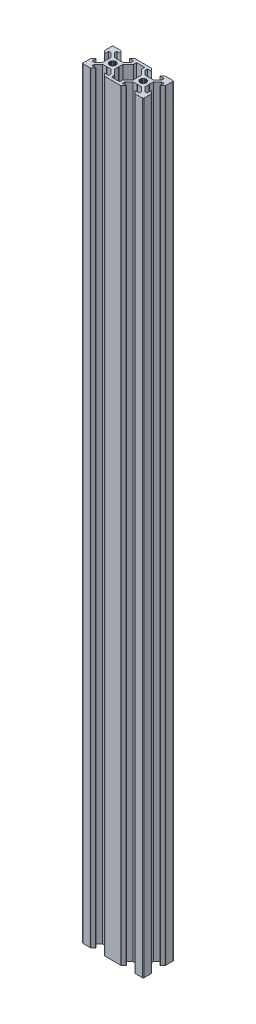
SolidWorks part; units mm, degrees
ref_plane "Alzado" through (0, 0, 0) normal (0, 0, 1) x (1, 0, 0)
ref_plane "Planta" through (0, 0, 0) normal (0, 1, 0) x (1, 0, 0)
ref_plane "Vista lateral" through (0, 0, 0) normal (1, 0, 0) x (0, 0, -1)
sketch "Croquis1" plane through (0, 0, 0) normal (0, 1, 0) x (1, 0, 0)
  line L0 (665.6997, 63.4231) -> (665.6997, 66.0554)
  line L1 (669.9997, 71.7624) -> (668.3603, 71.7624)
  line L2 (631.7997, 57.7624) -> (631.7997, 61.431)
  line L3 (631.801, 61.4707) -> (631.7997, 61.431)
  line L4 (631.8049, 61.5102) -> (631.801, 61.4707)
  line L5 (631.8113, 61.5494) -> (631.8049, 61.5102)
  line L6 (631.8204, 61.5881) -> (631.8113, 61.5494)
  line L7 (631.8319, 61.6261) -> (631.8204, 61.5881)
  line L8 (631.8459, 61.6633) -> (631.8319, 61.6261)
  line L9 (631.8623, 61.6995) -> (631.8459, 61.6633)
  line L10 (631.881, 61.7345) -> (631.8623, 61.6995)
  line L11 (631.902, 61.7682) -> (631.881, 61.7345)
  line L12 (631.9251, 61.8005) -> (631.902, 61.7682)
  line L13 (631.9503, 61.8312) -> (631.9251, 61.8005)
  line L14 (631.9775, 61.8602) -> (631.9503, 61.8312)
  line L15 (631.9775, 61.8602) -> (633.493, 63.3758)
  line L16 (633.493, 63.3758) -> (633.5997, 63.3758)
  line L17 (633.5997, 63.3758) -> (633.5997, 60.7624)
  line L18 (633.5997, 60.7624) -> (635.239, 60.7624)
  line L19 (635.239, 60.7624) -> (637.8997, 63.4231)
  line L20 (637.8997, 63.4231) -> (637.8997, 66.0554)
  line L21 (637.8997, 66.0554) -> (638.1067, 66.2624)
  line L22 (637.8997, 66.4694) -> (638.1067, 66.2624)
  line L23 (637.8997, 69.1018) -> (637.8997, 66.4694)
  line L24 (637.8997, 69.1018) -> (635.239, 71.7624)
  line L25 (633.5997, 71.7624) -> (635.239, 71.7624)
  line L26 (633.5997, 69.149) -> (633.5997, 71.7624)
  line L27 (633.493, 69.149) -> (633.5997, 69.149)
  line L28 (633.493, 69.149) -> (631.9775, 70.6646)
  line L29 (631.9775, 70.6646) -> (631.9503, 70.6936)
  line L30 (631.9503, 70.6936) -> (631.9251, 70.7243)
  line L31 (631.9251, 70.7243) -> (631.902, 70.7566)
  line L32 (633.2997, 56.2624) -> (636.8997, 56.2624)
  line L33 (631.902, 70.7566) -> (631.881, 70.7903)
  line L34 (637.0079, 56.2637) -> (636.8997, 56.2624)
  line L35 (631.881, 70.7903) -> (631.8623, 70.8254)
  line L36 (637.0475, 56.2676) -> (637.0079, 56.2637)
  line L37 (631.8623, 70.8254) -> (631.8459, 70.8616)
  line L38 (637.0867, 56.2741) -> (637.0475, 56.2676)
  line L39 (631.8459, 70.8616) -> (631.8319, 70.8987)
  line L40 (637.1253, 56.2831) -> (637.0867, 56.2741)
  line L41 (631.8319, 70.8987) -> (631.8204, 70.9368)
  line L42 (637.1634, 56.2946) -> (637.1253, 56.2831)
  line L43 (631.8204, 70.9368) -> (631.8113, 70.9754)
  line L44 (637.2005, 56.3086) -> (637.1634, 56.2946)
  line L45 (631.8113, 70.9754) -> (631.8049, 71.0146)
  line L46 (637.2367, 56.325) -> (637.2005, 56.3086)
  line L47 (631.8049, 71.0146) -> (631.801, 71.0542)
  line L48 (637.2718, 56.3438) -> (637.2367, 56.325)
  line L49 (631.801, 71.0542) -> (631.7997, 71.0939)
  line L50 (637.3055, 56.3647) -> (637.2718, 56.3438)
  line L51 (631.7997, 74.7624) -> (631.7997, 71.0939)
  line L52 (637.3378, 56.3879) -> (637.3055, 56.3647)
  line L53 (637.3685, 56.4131) -> (637.3378, 56.3879)
  line L54 (637.3975, 56.4402) -> (637.3685, 56.4131)
  line L55 (638.913, 57.9558) -> (637.3975, 56.4402)
  line L56 (638.913, 57.9558) -> (638.913, 58.0624)
  line L57 (638.913, 58.0624) -> (636.2997, 58.0624)
  line L58 (636.2997, 58.0624) -> (636.2997, 59.7018)
  line L59 (636.2997, 59.7018) -> (638.9603, 62.3624)
  line L60 (638.9603, 62.3624) -> (641.5998, 62.3624)
  line L61 (641.7997, 62.5623) -> (641.5998, 62.3624)
  line L62 (641.7997, 62.5623) -> (641.9995, 62.3624)
  line L63 (641.9995, 62.3624) -> (644.639, 62.3624)
  line L64 (647.2997, 59.7018) -> (644.639, 62.3624)
  line L65 (633.2997, 76.2624) -> (636.9682, 76.2624)
  line L66 (647.2997, 58.0624) -> (647.2997, 59.7018)
  line L67 (637.0079, 76.2611) -> (636.9682, 76.2624)
  line L68 (644.6863, 58.0624) -> (647.2997, 58.0624)
  line L69 (637.0475, 76.2572) -> (637.0079, 76.2611)
  line L70 (644.6863, 57.9558) -> (644.6863, 58.0624)
  line L71 (637.0867, 76.2508) -> (637.0475, 76.2572)
  line L72 (646.2019, 56.4402) -> (644.6863, 57.9558)
  line L73 (637.1253, 76.2417) -> (637.0867, 76.2508)
  line L74 (646.2019, 56.4402) -> (646.2309, 56.4131)
  line L75 (637.1634, 76.2302) -> (637.1253, 76.2417)
  line L76 (637.2005, 76.2162) -> (637.1634, 76.2302)
  line L77 (646.2309, 56.4131) -> (646.2616, 56.3879)
  line L78 (646.2616, 56.3879) -> (646.2939, 56.3647)
  line L79 (637.2367, 76.1998) -> (637.2005, 76.2162)
  line L80 (646.2939, 56.3647) -> (646.3276, 56.3438)
  line L81 (637.2718, 76.1811) -> (637.2367, 76.1998)
  line L82 (646.3276, 56.3438) -> (646.3626, 56.325)
  line L83 (637.3055, 76.1601) -> (637.2718, 76.1811)
  line L84 (646.3626, 56.325) -> (646.3988, 56.3086)
  line L85 (637.3378, 76.137) -> (637.3055, 76.1601)
  line L86 (646.3988, 56.3086) -> (646.436, 56.2946)
  line L87 (637.3685, 76.1118) -> (637.3378, 76.137)
  line L88 (646.436, 56.2946) -> (646.474, 56.2831)
  line L89 (637.3975, 76.0846) -> (637.3685, 76.1118)
  line L90 (646.474, 56.2831) -> (646.5127, 56.2741)
  line L91 (637.3975, 76.0846) -> (638.913, 74.569)
  line L92 (646.5127, 56.2741) -> (646.5519, 56.2676)
  line L93 (638.913, 74.569) -> (638.913, 74.4624)
  line L94 (646.5519, 56.2676) -> (646.5914, 56.2637)
  line L95 (638.913, 74.4624) -> (636.2997, 74.4624)
  line L96 (646.5914, 56.2637) -> (646.6997, 56.2624)
  line L97 (636.2997, 74.4624) -> (636.2997, 72.8231)
  line L98 (646.6997, 56.2624) -> (656.8997, 56.2624)
  line L99 (636.2997, 72.8231) -> (638.9603, 70.1624)
  line L100 (657.0079, 56.2637) -> (656.8997, 56.2624)
  line L101 (638.9603, 70.1624) -> (641.5998, 70.1624)
  line L102 (657.0475, 56.2676) -> (657.0079, 56.2637)
  line L103 (641.7997, 69.9626) -> (641.5998, 70.1624)
  line L104 (657.0867, 56.2741) -> (657.0475, 56.2676)
  line L105 (641.7997, 69.9626) -> (641.9995, 70.1624)
  line L106 (657.1253, 56.2831) -> (657.0867, 56.2741)
  line L107 (644.639, 70.1624) -> (641.9995, 70.1624)
  line L108 (657.1634, 56.2946) -> (657.1253, 56.2831)
  line L109 (647.2997, 72.8231) -> (644.639, 70.1624)
  line L110 (647.2997, 74.4624) -> (647.2997, 72.8231)
  line L111 (657.2005, 56.3086) -> (657.1634, 56.2946)
  line L112 (657.2367, 56.325) -> (657.2005, 56.3086)
  line L113 (644.6863, 74.4624) -> (647.2997, 74.4624)
  line L114 (657.2718, 56.3438) -> (657.2367, 56.325)
  line L115 (644.6863, 74.569) -> (644.6863, 74.4624)
  line L116 (657.3055, 56.3647) -> (657.2718, 56.3438)
  line L117 (644.6863, 74.569) -> (646.2019, 76.0846)
  line L118 (657.3378, 56.3879) -> (657.3055, 56.3647)
  line L119 (646.2019, 76.0846) -> (646.2309, 76.1118)
  line L120 (657.3685, 56.4131) -> (657.3378, 56.3879)
  line L121 (646.2309, 76.1118) -> (646.2616, 76.137)
  line L122 (657.3975, 56.4402) -> (657.3685, 56.4131)
  line L123 (646.2616, 76.137) -> (646.2939, 76.1601)
  line L124 (657.3975, 56.4402) -> (658.913, 57.9558)
  line L125 (646.2939, 76.1601) -> (646.3276, 76.1811)
  line L126 (658.913, 57.9558) -> (658.913, 58.0624)
  line L127 (646.3276, 76.1811) -> (646.3626, 76.1998)
  line L128 (658.913, 58.0624) -> (656.2997, 58.0624)
  line L129 (646.3626, 76.1998) -> (646.3988, 76.2162)
  line L130 (656.2997, 58.0624) -> (656.2997, 59.7018)
  line L131 (646.3988, 76.2162) -> (646.436, 76.2302)
  line L132 (656.2997, 59.7018) -> (658.9603, 62.3624)
  line L133 (646.436, 76.2302) -> (646.474, 76.2417)
  line L134 (661.5998, 62.3624) -> (658.9603, 62.3624)
  line L135 (646.474, 76.2417) -> (646.5127, 76.2508)
  line L136 (661.7997, 62.5623) -> (661.5998, 62.3624)
  line L137 (646.5127, 76.2508) -> (646.5519, 76.2572)
  line L138 (661.7997, 62.5623) -> (661.9995, 62.3624)
  line L139 (646.5519, 76.2572) -> (646.5914, 76.2611)
  line L140 (664.639, 62.3624) -> (661.9995, 62.3624)
  line L141 (646.5914, 76.2611) -> (646.6997, 76.2624)
  line L142 (667.2997, 59.7018) -> (664.639, 62.3624)
  line L143 (646.6997, 76.2624) -> (656.8997, 76.2624)
  line L144 (667.2997, 58.0624) -> (667.2997, 59.7018)
  line L145 (664.6863, 57.9558) -> (666.2019, 56.4402)
  line L146 (657.0079, 76.2611) -> (656.8997, 76.2624)
  line L147 (664.6863, 58.0624) -> (667.2997, 58.0624)
  line L148 (657.0475, 76.2572) -> (657.0079, 76.2611)
  line L149 (664.6863, 57.9558) -> (664.6863, 58.0624)
  line L150 (657.0867, 76.2508) -> (657.0475, 76.2572)
  line L151 (666.2019, 56.4402) -> (666.2309, 56.4131)
  line L152 (657.1253, 76.2417) -> (657.0867, 76.2508)
  line L153 (666.2309, 56.4131) -> (666.2616, 56.3879)
  line L154 (657.1634, 76.2302) -> (657.1253, 76.2417)
  line L155 (666.2616, 56.3879) -> (666.2939, 56.3647)
  line L156 (657.2005, 76.2162) -> (657.1634, 76.2302)
  line L157 (666.2939, 56.3647) -> (666.3276, 56.3438)
  line L158 (657.2367, 76.1998) -> (657.2005, 76.2162)
  line L159 (666.3276, 56.3438) -> (666.3626, 56.325)
  line L160 (657.2718, 76.1811) -> (657.2367, 76.1998)
  line L161 (666.3626, 56.325) -> (666.3988, 56.3086)
  line L162 (657.3055, 76.1601) -> (657.2718, 76.1811)
  line L163 (666.3988, 56.3086) -> (666.436, 56.2946)
  line L164 (657.3378, 76.137) -> (657.3055, 76.1601)
  line L165 (666.436, 56.2946) -> (666.474, 56.2831)
  line L166 (657.3685, 76.1118) -> (657.3378, 76.137)
  line L167 (666.474, 56.2831) -> (666.5127, 56.2741)
  line L168 (657.3975, 76.0846) -> (657.3685, 76.1118)
  line L169 (666.5127, 56.2741) -> (666.5519, 56.2676)
  line L170 (658.913, 74.569) -> (657.3975, 76.0846)
  line L171 (666.5519, 56.2676) -> (666.5914, 56.2637)
  line L172 (658.913, 74.569) -> (658.913, 74.4624)
  line L173 (666.5914, 56.2637) -> (666.6997, 56.2624)
  line L174 (656.2997, 72.8231) -> (658.9603, 70.1624)
  line L175 (658.913, 74.4624) -> (656.2997, 74.4624)
  line L176 (670.2997, 56.2624) -> (666.6997, 56.2624)
  line L177 (656.2997, 74.4624) -> (656.2997, 72.8231)
  line L178 (658.9603, 70.1624) -> (661.5998, 70.1624)
  line L179 (661.7997, 69.9626) -> (661.5998, 70.1624)
  line L180 (661.7997, 69.9626) -> (661.9995, 70.1624)
  line L181 (664.639, 70.1624) -> (661.9995, 70.1624)
  line L182 (667.2997, 72.8231) -> (664.639, 70.1624)
  line L183 (667.2997, 74.4624) -> (667.2997, 72.8231)
  line L184 (664.6863, 74.4624) -> (667.2997, 74.4624)
  line L185 (664.6863, 74.569) -> (664.6863, 74.4624)
  line L186 (666.2019, 76.0846) -> (664.6863, 74.569)
  line L187 (666.2019, 76.0846) -> (666.2309, 76.1118)
  line L188 (666.2309, 76.1118) -> (666.2616, 76.137)
  line L189 (671.7997, 57.7624) -> (671.7997, 61.431)
  line L190 (666.2616, 76.137) -> (666.2939, 76.1601)
  line L191 (671.7984, 61.4707) -> (671.7997, 61.431)
  line L192 (666.2939, 76.1601) -> (666.3276, 76.1811)
  line L193 (671.7945, 61.5102) -> (671.7984, 61.4707)
  line L194 (666.3276, 76.1811) -> (666.3626, 76.1998)
  line L195 (671.788, 61.5494) -> (671.7945, 61.5102)
  line L196 (666.3626, 76.1998) -> (666.3988, 76.2162)
  line L197 (671.779, 61.5881) -> (671.788, 61.5494)
  line L198 (666.3988, 76.2162) -> (666.436, 76.2302)
  line L199 (671.7675, 61.6261) -> (671.779, 61.5881)
  line L200 (666.436, 76.2302) -> (666.474, 76.2417)
  line L201 (671.7371, 61.6995) -> (671.7535, 61.6633)
  line L202 (671.7535, 61.6633) -> (671.7675, 61.6261)
  line L203 (666.474, 76.2417) -> (666.5127, 76.2508)
  line L204 (671.7183, 61.7345) -> (671.7371, 61.6995)
  line L205 (666.5127, 76.2508) -> (666.5519, 76.2572)
  line L206 (671.6974, 61.7682) -> (671.7183, 61.7345)
  line L207 (666.5519, 76.2572) -> (666.5914, 76.2611)
  line L208 (671.6742, 61.8005) -> (671.6974, 61.7682)
  line L209 (666.5914, 76.2611) -> (666.6311, 76.2624)
  line L210 (671.649, 61.8312) -> (671.6742, 61.8005)
  line L211 (670.2997, 76.2624) -> (666.6311, 76.2624)
  line L212 (671.6219, 61.8602) -> (671.649, 61.8312)
  line L213 (671.6219, 61.8602) -> (670.1063, 63.3758)
  line L214 (670.1063, 63.3758) -> (669.9997, 63.3758)
  line L215 (669.9997, 63.3758) -> (669.9997, 60.7624)
  line L216 (669.9997, 60.7624) -> (668.3603, 60.7624)
  line L217 (668.3603, 60.7624) -> (665.6997, 63.4231)
  line L218 (657.8997, 66.4694) -> (657.8997, 69.1018)
  line L219 (657.8997, 63.4231) -> (657.8997, 66.0577)
  line L220 (654.4997, 60.0231) -> (657.8997, 63.4231)
  line L221 (654.4997, 58.0624) -> (654.4997, 60.0231)
  line L222 (654.4997, 58.0624) -> (649.0997, 58.0624)
  line L223 (649.0997, 58.0624) -> (649.0997, 60.0231)
  line L224 (649.0997, 60.0231) -> (645.6997, 63.4231)
  line L225 (645.6997, 63.4231) -> (645.6997, 66.0554)
  line L226 (645.6997, 66.0554) -> (645.4927, 66.2624)
  line L227 (645.4927, 66.2624) -> (645.6997, 66.4694)
  line L228 (645.6997, 66.4694) -> (645.6997, 69.1018)
  line L229 (645.6997, 69.1018) -> (649.0997, 72.5018)
  line L230 (671.7997, 74.7624) -> (671.7997, 71.0939)
  line L231 (671.7984, 71.0542) -> (671.7997, 71.0939)
  line L232 (671.788, 70.9754) -> (671.7945, 71.0146)
  line L233 (671.779, 70.9368) -> (671.788, 70.9754)
  line L234 (671.7945, 71.0146) -> (671.7984, 71.0542)
  line L235 (671.7535, 70.8616) -> (671.7675, 70.8987)
  line L236 (671.7371, 70.8254) -> (671.7535, 70.8616)
  line L237 (671.6974, 70.7566) -> (671.7183, 70.7903)
  line L238 (671.7675, 70.8987) -> (671.779, 70.9368)
  line L239 (670.1063, 69.149) -> (669.9997, 69.149)
  line L240 (671.6219, 70.6646) -> (671.649, 70.6936)
  line L241 (671.7183, 70.7903) -> (671.7371, 70.8254)
  line L242 (671.649, 70.6936) -> (671.6742, 70.7243)
  line L243 (671.6742, 70.7243) -> (671.6974, 70.7566)
  line L244 (669.9997, 69.149) -> (669.9997, 71.7624)
  line L245 (670.1063, 69.149) -> (671.6219, 70.6646)
  line L246 (665.6997, 69.1018) -> (665.6997, 66.4694)
  line L247 (665.6997, 69.1018) -> (668.3603, 71.7624)
  line L248 (649.0997, 72.5018) -> (649.0997, 74.4624)
  line L249 (649.0997, 74.4624) -> (654.4997, 74.4624)
  line L250 (654.4997, 72.5018) -> (654.4997, 74.4624)
  line L251 (657.8997, 69.1018) -> (654.4997, 72.5018)
  line L252 (658.1044, 66.2624) -> (657.8997, 66.4694)
  line L253 (657.8997, 66.0577) -> (658.1044, 66.2624)
  line L254 (665.6997, 66.0554) -> (665.4927, 66.2624)
  line L255 (665.6997, 66.4694) -> (665.4927, 66.2624)
  line L256 (639.981, 65.2124) -> (640.3148, 64.7775)
  line L257 (639.7712, 65.7189) -> (639.981, 65.2124)
  line L258 (639.6997, 66.2624) -> (639.7712, 65.7189)
  line L259 (639.7712, 66.8059) -> (639.6997, 66.2624)
  line L260 (639.981, 67.3124) -> (639.7712, 66.8059)
  line L261 (640.3148, 67.7473) -> (639.981, 67.3124)
  line L262 (640.7497, 68.0811) -> (640.3148, 67.7473)
  line L263 (641.2562, 68.2909) -> (640.7497, 68.0811)
  line L264 (641.7997, 68.3624) -> (641.2562, 68.2909)
  line L265 (642.3432, 68.2909) -> (641.7997, 68.3624)
  line L266 (642.8497, 68.0811) -> (642.3432, 68.2909)
  line L267 (643.2846, 67.7473) -> (642.8497, 68.0811)
  line L268 (643.6183, 67.3124) -> (643.2846, 67.7473)
  line L269 (643.8281, 66.8059) -> (643.6183, 67.3124)
  line L270 (643.8997, 66.2624) -> (643.8281, 66.8059)
  line L271 (643.8281, 65.7189) -> (643.8997, 66.2624)
  line L272 (643.6183, 65.2124) -> (643.8281, 65.7189)
  line L273 (643.2846, 64.7775) -> (643.6183, 65.2124)
  line L274 (642.8497, 64.4438) -> (643.2846, 64.7775)
  line L275 (642.3432, 64.234) -> (642.8497, 64.4438)
  line L276 (641.7997, 64.1624) -> (642.3432, 64.234)
  line L277 (641.2562, 64.234) -> (641.7997, 64.1624)
  line L278 (640.7497, 64.4438) -> (641.2562, 64.234)
  line L279 (640.3148, 64.7775) -> (640.7497, 64.4438)
  line L280 (659.981, 65.2124) -> (660.3148, 64.7775)
  line L281 (659.7712, 65.7189) -> (659.981, 65.2124)
  line L282 (659.6997, 66.2624) -> (659.7712, 65.7189)
  line L283 (659.7712, 66.8059) -> (659.6997, 66.2624)
  line L284 (659.981, 67.3124) -> (659.7712, 66.8059)
  line L285 (660.3148, 67.7473) -> (659.981, 67.3124)
  line L286 (660.7497, 68.0811) -> (660.3148, 67.7473)
  line L287 (661.2562, 68.2909) -> (660.7497, 68.0811)
  line L288 (661.7997, 68.3624) -> (661.2562, 68.2909)
  line L289 (662.3432, 68.2909) -> (661.7997, 68.3624)
  line L290 (662.8497, 68.0811) -> (662.3432, 68.2909)
  line L291 (663.2846, 67.7473) -> (662.8497, 68.0811)
  line L292 (663.6183, 67.3124) -> (663.2846, 67.7473)
  line L293 (663.8281, 66.8059) -> (663.6183, 67.3124)
  line L294 (663.8997, 66.2624) -> (663.8281, 66.8059)
  line L295 (663.8281, 65.7189) -> (663.8997, 66.2624)
  line L296 (663.6183, 65.2124) -> (663.8281, 65.7189)
  line L297 (663.2846, 64.7775) -> (663.6183, 65.2124)
  line L298 (662.8497, 64.4438) -> (663.2846, 64.7775)
  line L299 (662.3432, 64.234) -> (662.8497, 64.4438)
  line L300 (661.7997, 64.1624) -> (662.3432, 64.234)
  line L301 (661.2562, 64.234) -> (661.7997, 64.1624)
  line L302 (660.7497, 64.4438) -> (661.2562, 64.234)
  line L303 (660.3148, 64.7775) -> (660.7497, 64.4438)
  line L304 (670.2997, 76.2624) -> (671.2997, 76.2624)
  line L305 (671.7997, 75.7624) -> (671.7997, 74.7624)
  line L306 (632.2997, 76.2624) -> (633.2997, 76.2624)
  line L307 (631.7997, 75.7624) -> (631.7997, 74.7624)
  line L308 (631.7997, 57.7624) -> (631.7997, 56.7624)
  line L309 (632.2997, 56.2624) -> (633.2997, 56.2624)
  line L310 (670.2997, 56.2624) -> (671.2997, 56.2624)
  line L311 (671.7997, 56.7624) -> (671.7997, 57.7624)
  arc A0 (671.7997, 75.7624) -> (671.2997, 76.2624) centre (671.2997, 75.7624) ccw
  arc A1 (671.2997, 56.2624) -> (671.7997, 56.7624) centre (671.2997, 56.7624) ccw
  arc A2 (631.7997, 56.7624) -> (632.2997, 56.2624) centre (632.2997, 56.7624) ccw
  arc A3 (632.2997, 76.2624) -> (631.7997, 75.7624) centre (632.2997, 75.7624) ccw
extrude "Saliente-Extruir1" add sketch "Croquis1" along normal blind 500
